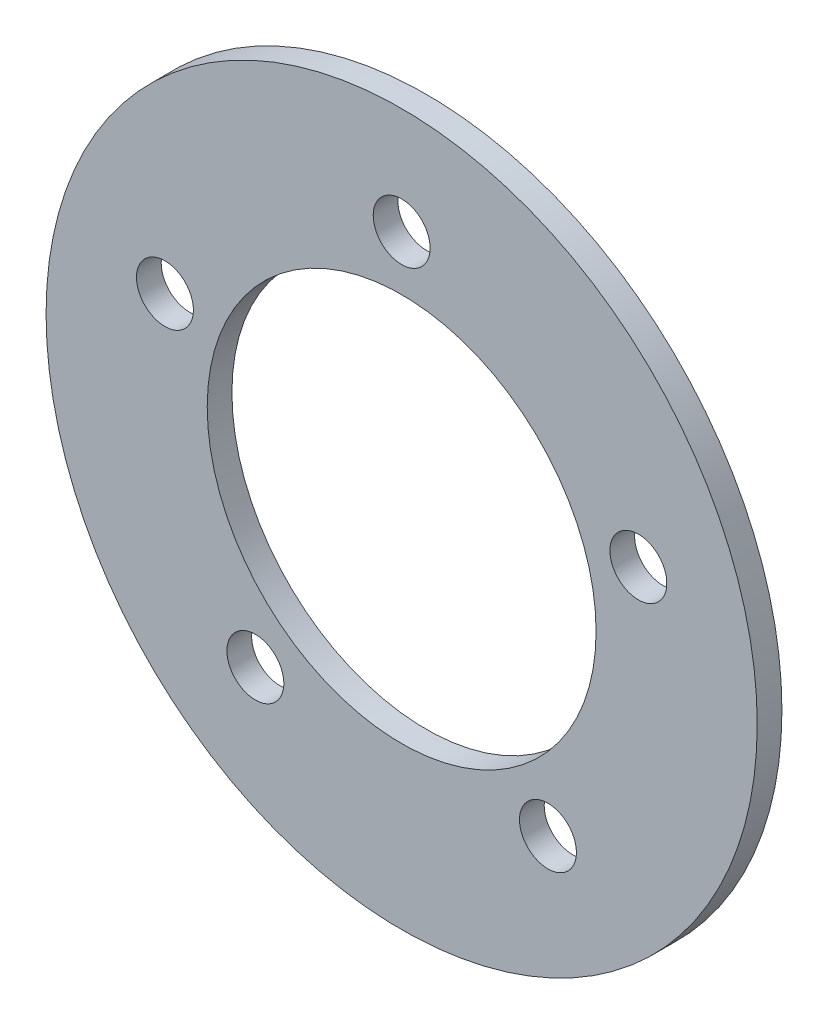
SolidWorks part; units mm, degrees
material "6061-T6 (SS)"
ref_plane "Front Plane" through (0, 0, 0) normal (0, 0, 1) x (1, 0, 0)
ref_plane "Top Plane" through (0, 0, 0) normal (0, 1, 0) x (1, 0, 0)
ref_plane "Right Plane" through (0, 0, 0) normal (1, 0, 0) x (0, 0, -1)
sketch "Sketch1" plane through (0, 0, -12.7) normal (0, 0, -1) x (-1, 0, 0)
  circle A1 centre (0, 0) radius 12.5
  circle A2 centre (0, 0) radius 22.86
  circle A3 centre (15.2169, 4.9443) radius 1.8288 construction
  circle A4 centre (9.4046, -12.9443) radius 1.8288 construction
  circle A5 centre (-9.4046, -12.9443) radius 1.8288 construction
  circle A6 centre (-15.2169, 4.9443) radius 1.8288 construction
  circle A7 centre (0, 16) radius 1.8288 construction
  circle A8 centre (15.2169, 4.9443) radius 1.8288
  circle A9 centre (9.4046, -12.9443) radius 1.8288
  circle A10 centre (-9.4046, -12.9443) radius 1.8288
  circle A11 centre (-15.2169, 4.9443) radius 1.8288
  circle A12 centre (0, 16) radius 1.8288
  circle A13 centre (0, 0) radius 12.5 construction
  dimension "D1" = 45.72
extrude "Boss-Extrude1" add sketch "Sketch1" along normal blind 1.5875
